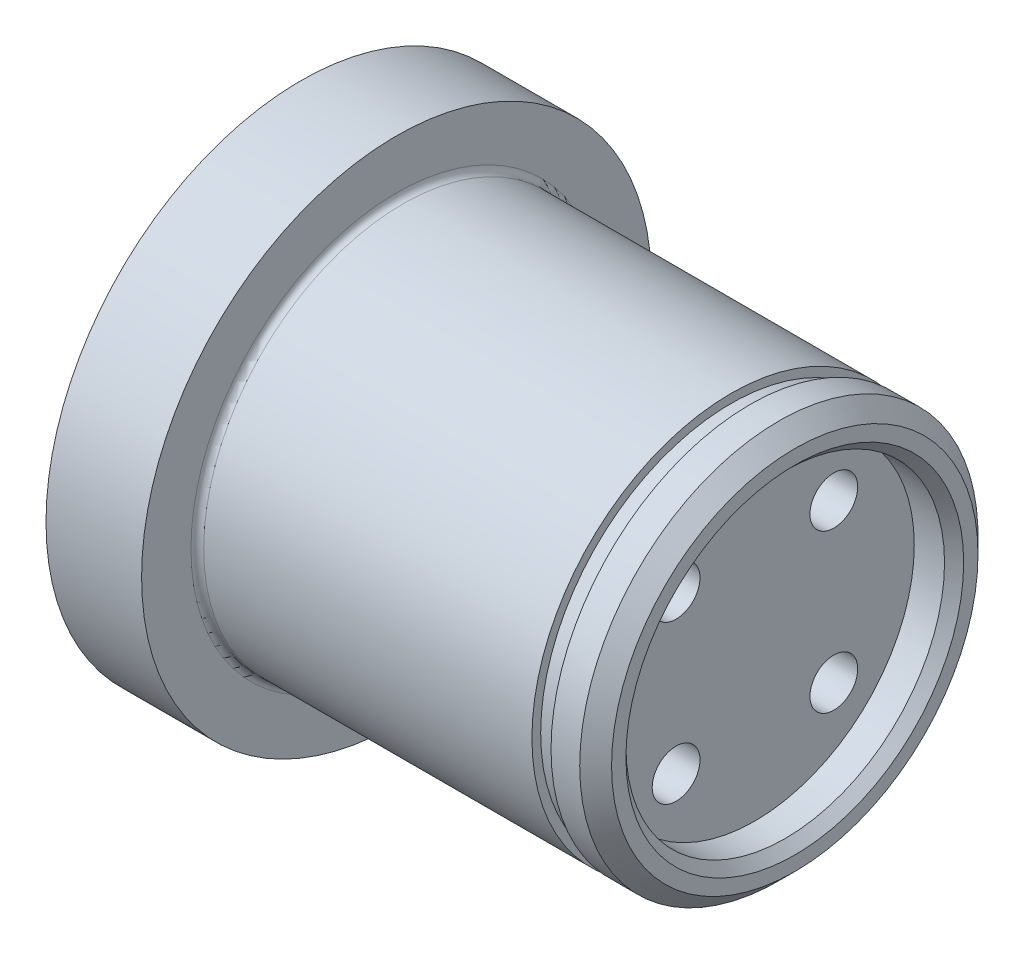
SolidWorks part; units mm, degrees
material "1060 Сплав"
ref_plane "Спереди" through (0, 0, 0) normal (0, 0, 1) x (1, 0, 0)
ref_plane "Сверху" through (0, 0, 0) normal (0, 1, 0) x (1, 0, 0)
ref_plane "Справа" through (0, 0, 0) normal (1, 0, 0) x (0, 0, -1)
sketch "Эскиз1" plane through (0, 0, 0) normal (0, 0, 1) x (1, 0, 0)
  line L0 (0, 0) -> (22138.4448, 0) construction
  line L1 (0, 0) -> (0, 12.5)
  line L2 (0, 12.5) -> (-25, 12.5)
  line L3 (-25, 12.5) -> (-25, 16)
  line L4 (-25, 16) -> (-31, 16)
  line L5 (-31, 16) -> (-31, 0)
  line L8 (0, 0) -> (-31, 0)
  dimension "D1" = 31
  dimension "D2" = 6
  dimension "D3" = 25
  dimension "D6" = 32
revolve "Повернуть1" add sketch "Эскиз1" angle 360 about L0
sketch "Эскиз2" plane through (0, 0, 0) normal (0, 0, 1) x (1, 0, 0)
  line L0 (-4, 12.5) -> (-4, 11.95)
  line L1 (0, 12.5) -> (-25, 12.5) construction
  line L2 (-4, 11.95) -> (-2.8, 11.95)
  line L3 (-2.8, 11.95) -> (-2.8, 12.5)
  line L4 (-2.8, 12.5) -> (-4, 12.5)
  line L5 (0, -12.5) -> (0, 12.5) construction
  line L6 (0, 0) -> (-50000, 0) construction
  point P10 (-2.8, 12.225)
  point P13 (0, 0)
  dimension "D1" = 4
  dimension "D2" = 1.2
  dimension "D3" = 23.9
revolve "Вырез-Повернуть1" cut sketch "Эскиз2" angle 360 about L6
chamfer "Фаска1" distance 1 angle 45 1 edges at (0, 0, 12.5)
fillet "Скругление1" radius 0.4 1 edges at (-25, 0, 12.5)
hole_wizard "Отверстие1" positions "Эскиз3" profile "Эскиз4" legacy
sketch "Эскиз3" plane through (0, 0, 0) normal (1, 0, 0) x (0, 0, -1)
  line L0 (0, 0) -> (0, 7) construction
  line L2 (0, 0) -> (4.9497, 4.9497) construction
  circle A0 centre (0, 0) radius 7 construction
  point P0 (4.9497, 4.9497)
  dimension "D1" = 14
  dimension "D2" = 45
sketch "Эскиз4" plane through (0, 4.9497, -4.9497) normal (0, 1, 0) x (0, 0, -1)
  line L0 (0, 0) -> (0, 15)
  line L1 (0, 15) -> (1.5, 15)
  line L2 (1.5, 15) -> (1.5, 0)
  line L3 (1.5, 0) -> (0, 0)
  line L4 (0, 110) -> (0, -10) construction
  dimension "Диаметр" = 3
  dimension "Глубина" = 15
pattern_circular "Круговой массив1" count 4 over 360 about axis through (0, 0, 0) along (1, 0, 0) of "Отверстие1"
sketch "Эскиз5" plane through (0, 0, 0) normal (0, 0, 1) x (1, 0, 0)
  line L0 (0, 0) -> (0, 10)
  line L1 (0, -11.5) -> (0, 11.5) construction
  line L7 (0, 10) -> (-2.5, 10)
  line L8 (-2.5, 10) -> (-2.5, 0)
  line L9 (-2.5, 0) -> (0, 0)
  line L10 (0, 0) -> (-50000, 0) construction
  dimension "D1" = 2.5
  dimension "D2" = 20
revolve "Вырез-Повернуть2" cut sketch "Эскиз5" angle 360 about L10
chamfer "Фаска2" distance 0.6 angle 45 1 edges at (0, 0, -10)
hole_wizard "Сверло под метчик  спиральное M31" positions "Эскиз6" profile "Эскиз7" hole size "M3x0.5" standard "DIN"
sketch "Эскиз6" plane through (-31, 0, 0) normal (-1, 0, 0) x (0, 0, 1)
  point P0 (-10, 0)
  point P12 (0, 0)
  point P13 (0, 0)
  point P15 (0, 0)
  dimension "D1" = 10
sketch "Эскиз7" plane through (-31, 0, -10) normal (0, 1, 0) x (0, 0, 1)
  line L0 (0, 0) -> (0, 20.9464)
  line L1 (0, 20.9464) -> (1.575, 20)
  line L2 (1.575, 20) -> (1.575, 0)
  line L5 (1.575, 0) -> (0, 0)
  line L10 (0, 20.9464) -> (-1.575, 20) construction
  line L11 (0, -6.35) -> (0, 107.95) construction
  dimension "Диаметр отверстия" = 3.15
  dimension "Глубина отверстия" = 20
  dimension "Угол заточки сверла" = 118
pattern_circular "Круговой массив2" count 4 over 360 about axis through (0, 0, 0) along (1, 0, 0) of "Сверло под метчик  спиральное M31"
